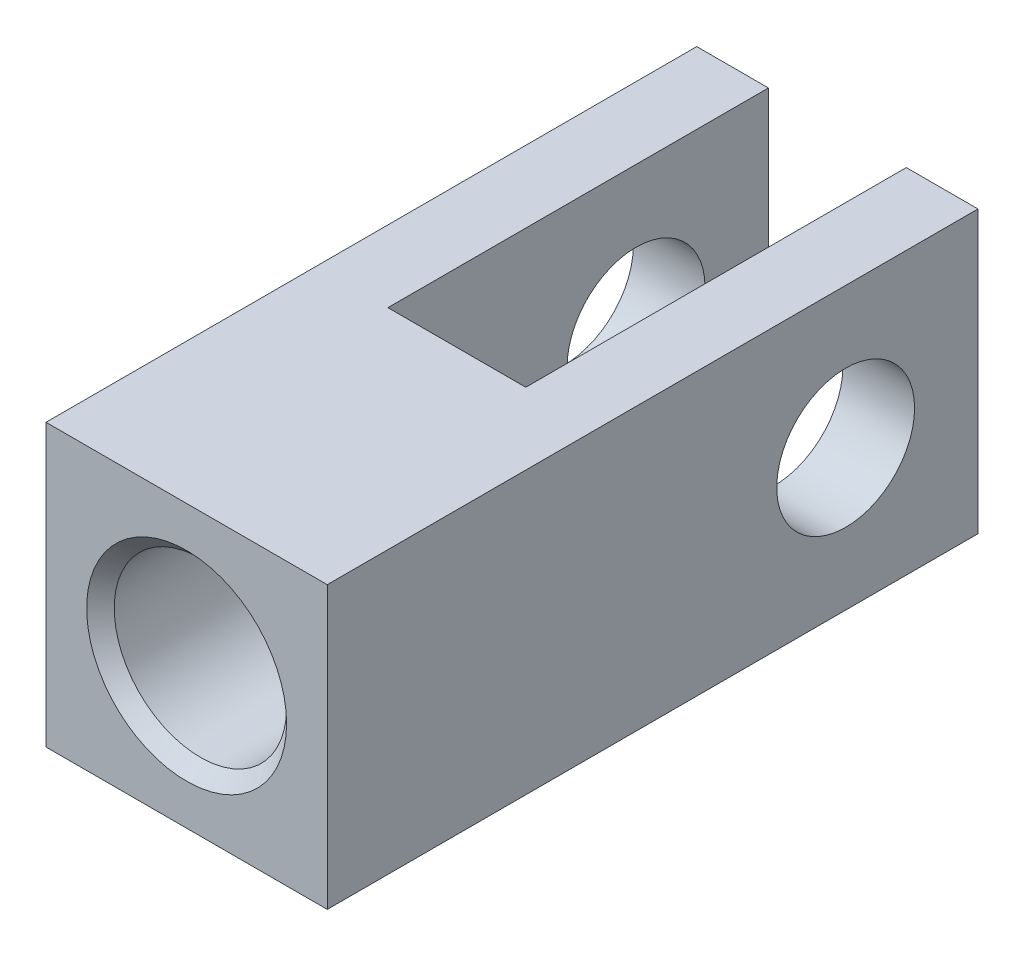
SolidWorks part; units mm, degrees
material "AISI 316 Annealed Stainless Steel Bar (SS)"
ref_plane "Front" through (0, 0, 0) normal (0, 0, 1) x (1, 0, 0)
ref_plane "Top" through (0, 0, 0) normal (0, 1, 0) x (1, 0, 0)
ref_plane "Right" through (0, 0, 0) normal (1, 0, 0) x (0, 0, -1)
sketch "Sketch1" plane through (0, 0, 0) normal (0, 1, 0) x (1, 0, 0)
  line L1 (6.477, -14.986) -> (-6.477, -14.986)
  line L2 (6.477, -14.986) -> (6.477, 14.986)
  line L3 (6.477, 14.986) -> (-6.477, 14.986)
  line L4 (-6.477, -14.986) -> (-6.477, 14.986)
  line L5 (6.477, -14.986) -> (-6.477, 14.986) construction
  line L6 (6.477, 14.986) -> (-6.477, -14.986) construction
  point P0 (0, 0)
  dimension "D" = 29.972
  dimension "G" = 12.954
extrude "Extrude1" add sketch "Sketch1" along normal mid plane 12.954
sketch "Sketch2" plane through (0, 6.477, 0) normal (0, 1, 0) x (1, 0, 0)
  line L0 (6.477, 14.986) -> (-6.477, 14.986) construction
  line L1 (-3.175, 14.986) -> (3.175, 14.986)
  line L2 (-3.175, 14.986) -> (-3.175, -2.54)
  line L3 (-3.175, -2.54) -> (3.175, -2.54)
  line L4 (3.175, 14.986) -> (3.175, -2.54)
  line L5 (0, -2.54) -> (0, 0) construction
  dimension "F" = 6.35
  dimension "E" = 17.526
extrude "Extrude2" cut sketch "Sketch2" against normal through all
sketch "Sketch5" plane through (6.477, 0, 0) normal (1, 0, 0) x (0, 0, -1)
  line L0 (0, 0) -> (8.89, 0) construction
  line L1 (-14.986, 6.477) -> (-14.986, -6.477) construction
  circle A0 centre (8.89, 0) radius 3.175
  dimension "J" = 6.35
  dimension "C" = 23.876
extrude "Extrude3" cut sketch "Sketch5" against normal through all
hole_wizard "1/4-28 Tapped Hole1" positions "Sketch4" profile "Sketch3" tap size "1/4-28" standard "Ansi Inch"
sketch "Sketch4" plane through (0, 0, 14.986) normal (0, 0, 1) x (1, 0, 0)
  point P0 (0, 0)
sketch "Sketch3" plane through (0, 0, 14.986) normal (1, 0, 0) x (0, -1, 0)
  line L0 (0, 0) -> (0, 17.0457)
  line L1 (0, 17.0457) -> (2.7051, 15.4203)
  line L2 (2.7051, 15.4203) -> (2.7051, 12.7)
  line L3 (2.7051, 12.7) -> (3.175, 12.7)
  line L5 (3.175, 12.7) -> (3.175, 0.1651)
  line L6 (3.175, 0.1651) -> (3.3401, 0)
  line L7 (3.3401, 0) -> (0, 0)
  line L8 (-3.175, 0.1651) -> (-3.3401, 0) construction
  line L10 (0, 17.0457) -> (-2.7051, 15.4203) construction
  line L11 (0, -6.35) -> (0, 107.95) construction
  dimension "Tap Drill Dia." = 5.4102
  dimension "Tap Drill Depth" = 15.4203
  dimension "Thread Major Dia." = 6.35
  dimension "Thread Depth" = 12.7
  dimension "Near C'Sink Dia." = 6.6802
  dimension "Near C'Sink Angle" = 90
  dimension "Drill Angle" = 118
hole_wizard "5/16-24 Tapped Hole1" positions "Sketch7" profile "Sketch8" tap size "5/16-24" standard "Ansi Inch" end condition up to next
sketch "Sketch7" plane through (0, 0, 14.986) normal (0, 0, 1) x (1, 0, 0)
  point P0 (0, 0)
sketch "Sketch8" plane through (0, 0, 14.986) normal (1, 0, 0) x (0, -1, 0)
  line L0 (0, 0) -> (0, 12.446)
  line L1 (0, 12.446) -> (3.9687, 12.446)
  line L2 (3.9687, 12.446) -> (3.9687, 0.635)
  line L3 (3.9687, 0.635) -> (4.6037, 0)
  line L5 (4.6037, 0) -> (0, 0)
  line L6 (-3.9687, 0.635) -> (-4.6037, 0) construction
  line L11 (0, -6.35) -> (0, 107.95) construction
  dimension "Thread Major Dia." = 7.9375
  dimension "Thru Tap Drill Depth" = 12.446
  dimension "Near C'Sink Dia." = 9.2075
  dimension "Near C'Sink Angle" = 90
hole_wizard "7/16-20 Tapped Hole1" positions "Sketch10" profile "Sketch9" tap size "7/16-20" standard "Ansi Inch"
sketch "Sketch10" plane through (0, 0, 21.463) normal (0, 0, 1) x (1, 0, 0)
  point P0 (0, 0)
sketch "Sketch9" plane through (0, 0, 21.463) normal (1, 0, 0) x (0, -1, 0)
  line L0 (0, 0) -> (0, 19.05)
  line L1 (0, 19.05) -> (5.5562, 19.05)
  line L2 (5.5562, 19.05) -> (5.5562, 0.635)
  line L3 (5.5562, 0.635) -> (6.1913, 0)
  line L5 (6.1913, 0) -> (0, 0)
  line L6 (-5.5562, 0.635) -> (-6.1913, 0) construction
  line L11 (0, -6.35) -> (0, 107.95) construction
  dimension "Thread Major Dia." = 11.1125
  dimension "Thru Tap Drill Depth" = 19.05
  dimension "Near C'Sink Dia." = 12.3825
  dimension "Near C'Sink Angle" = 90
hole_wizard "1/2-20 Tapped Hole1" positions "Sketch12" profile "Sketch13" tap size "1/2-20" standard "Ansi Inch"
sketch "Sketch12" plane through (0, 0, 21.463) normal (0, 0, 1) x (1, 0, 0)
  point P0 (0, 0)
sketch "Sketch13" plane through (0, 0, 21.463) normal (1, 0, 0) x (0, -1, 0)
  line L0 (0, 0) -> (0, 19.05)
  line L1 (0, 19.05) -> (6.35, 19.05)
  line L2 (6.35, 19.05) -> (6.35, 0.635)
  line L3 (6.35, 0.635) -> (6.985, 0)
  line L5 (6.985, 0) -> (0, 0)
  line L6 (-6.35, 0.635) -> (-6.985, 0) construction
  line L11 (0, -6.35) -> (0, 107.95) construction
  dimension "Thread Major Dia." = 12.7
  dimension "Thru Tap Drill Depth" = 19.05
  dimension "Near C'Sink Dia." = 13.97
  dimension "Near C'Sink Angle" = 90
hole_wizard "#10-32 Tapped Hole1" positions "3DSketch1" profile "Sketch15" tap size "#10-32" standard "Ansi Inch"
sketch3d "3DSketch1"
  line L0 (-4.826, 0, 11.938) -> (4.826, 0, 11.938) construction
  line L1 (-4.826, 4.826, 11.938) -> (-4.826, -4.826, 11.938) construction
  line L2 (4.826, 4.826, 11.938) -> (4.826, -4.826, 11.938) construction
  line L4 (0, 4.826, 11.938) -> (0, -4.826, 11.938) construction
  line L5 (-4.826, 4.826, 11.938) -> (4.826, 4.826, 11.938) construction
  line L6 (-4.826, -4.826, 11.938) -> (4.826, -4.826, 11.938) construction
  point P26 (0, 0, 0)
  point P30 (0, 0, 11.938)
sketch "Sketch15" plane through (0, 0, 11.938) normal (1, 0, 0) x (0, -1, 0)
  line L0 (0, 0) -> (0, 9.653)
  line L1 (0, 9.653) -> (2.413, 9.653)
  line L2 (2.413, 9.653) -> (2.413, 0.127)
  line L3 (2.413, 0.127) -> (2.54, 0)
  line L5 (2.54, 0) -> (0, 0)
  line L6 (-2.413, 0.127) -> (-2.54, 0) construction
  line L11 (0, -6.35) -> (0, 107.95) construction
  dimension "Thread Major Dia." = 4.826
  dimension "Thru Tap Drill Depth" = 9.653
  dimension "Near C'Sink Dia." = 5.08
  dimension "Near C'Sink Angle" = 90
